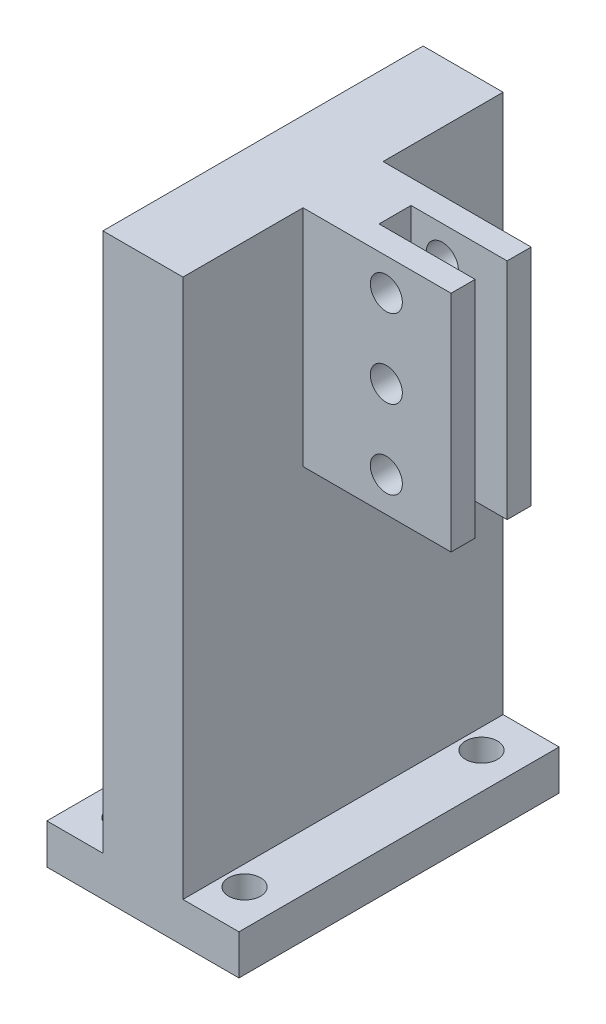
SolidWorks part; units mm, degrees
ref_plane "Front" through (0, 0, 0) normal (0, 0, 1) x (1, 0, 0)
ref_plane "Top" through (0, 0, 0) normal (0, 1, 0) x (1, 0, 0)
ref_plane "Right" through (0, 0, 0) normal (1, 0, 0) x (0, 0, -1)
sketch "草图1" plane through (0, 0, 0) normal (0, 1, 0) x (1, 0, 0)
  line L0 (0, 0) -> (0, -14.8) construction
  line L1 (-20, 20) -> (20, 20) construction
  line L2 (20, 20) -> (20, -20) construction
  line L3 (20, 0) -> (0, 0) construction
  line L4 (0, 0) -> (0, 20) construction
  line L5 (0, 20) -> (12, 20) construction
  line L6 (-20, 20) -> (-20, -20) construction
  line L7 (-20, -20) -> (20, -20) construction
  line L12 (0, -14.8) -> (7.5, -14.8) construction
  line L13 (0, -14.8) -> (-7.5, -14.8) construction
  line L14 (12, 20) -> (12, -20) construction
  line L15 (12, -20) -> (-12, -20)
  line L16 (12, -20) -> (12, 20)
  line L17 (12, 20) -> (-12, 20)
  line L18 (-12, -20) -> (-12, 20)
  circle A4 centre (7.5, -14.8) radius 2
  circle A5 centre (-7.5, -14.8) radius 2
  circle A6 centre (-7.5, 14.8) radius 2
  circle A7 centre (7.5, 14.8) radius 2
  point P13 (10, 0)
  point P14 (-10, 0)
  point P16 (-20, 0)
  point P22 (12, 0)
  point P26 (0, -20)
extrude "凸台-拉伸1" add sketch "草图1" along normal blind 5
sketch "草图8" plane through (0, 5, 0) normal (0, 1, 0) x (1, 0, 0)
  line L0 (0, 0) -> (5, 0) construction
  line L1 (0, 0) -> (-5, 0) construction
  line L2 (-5, 0) -> (-5, -20)
  line L3 (-12, -20) -> (12, -20) construction
  line L4 (-5, -20) -> (5, -20)
  line L5 (5, -20) -> (5, 20)
  line L6 (12, 20) -> (-12, 20) construction
  line L7 (5, 20) -> (-5, 20)
  line L8 (-5, 20) -> (-5, 0)
  line L9 (5, 20) -> (12, 20) construction
extrude "凸台-拉伸5" add sketch "草图8" along normal blind 67.34
sketch "草图10" plane through (5, 0, 0) normal (1, 0, 0) x (0, 0, -1)
  line L0 (0, 72.34) -> (5, 72.34) construction
  line L1 (-20, 72.34) -> (20, 72.34) construction
  line L2 (5, 72.34) -> (5, 44.34) construction
  line L3 (5, 44.34) -> (-5, 44.34) construction
  line L4 (-5, 44.34) -> (-5, 72.34) construction
  line L5 (-5, 72.34) -> (0, 72.34) construction
  line L6 (-5, 72.34) -> (5, 72.34)
  line L7 (5, 72.34) -> (5, 44.34)
  line L8 (5, 44.34) -> (-5, 44.34)
  line L9 (-5, 44.34) -> (-5, 72.34)
extrude "凸台-拉伸6" add sketch "草图10" along normal blind 18.5
sketch "草图12" plane through (0, 0, -5) normal (0, 0, -1) x (-1, 0, 0)
  line L0 (-23.5, 72.34) -> (-11.5, 72.34) construction
  line L1 (-23.5, 72.34) -> (-5, 72.34) construction
  line L2 (-17.5, 68.31) -> (-17.5, 58.49) construction
  line L3 (-17.5, 68.31) -> (-21.41, 68.31) construction
  line L4 (-17.5, 58.49) -> (-21.41, 58.49) construction
  line L5 (-21.41, 58.49) -> (-21.41, 48.67) construction
  line L6 (-11.5, 72.34) -> (-11.5, 68.31) construction
  line L7 (-11.5, 68.31) -> (-15.41, 68.31) construction
  line L8 (-15.41, 68.31) -> (-15.41, 58.49) construction
  line L9 (-15.41, 58.49) -> (-11.5, 58.49) construction
  line L10 (-11.5, 58.49) -> (-11.5, 48.67) construction
  line L11 (-11.5, 48.67) -> (-15.41, 48.67) construction
  circle A3 centre (-15.41, 68.31) radius 2
  circle A4 centre (-15.41, 58.49) radius 2
  circle A5 centre (-15.41, 48.67) radius 2
extrude "切除-拉伸4" cut sketch "草图12" against normal blind 24.5
sketch "草图13" plane through (0, 0, 0) normal (0, 0, 1) x (1, 0, 0)
  line L0 (23.5, 72.34) -> (11.5, 72.34)
  line L1 (23.5, 72.34) -> (5, 72.34) construction
  line L5 (23.5, 44.34) -> (23.5, 72.34)
  line L6 (11.5, 72.34) -> (11.5, 44.34)
  line L7 (23.5, 44.34) -> (5, 44.34) construction
  line L8 (11.5, 44.34) -> (23.5, 44.34)
extrude "切除-拉伸5" cut sketch "草图13" against normal mid plane 4
